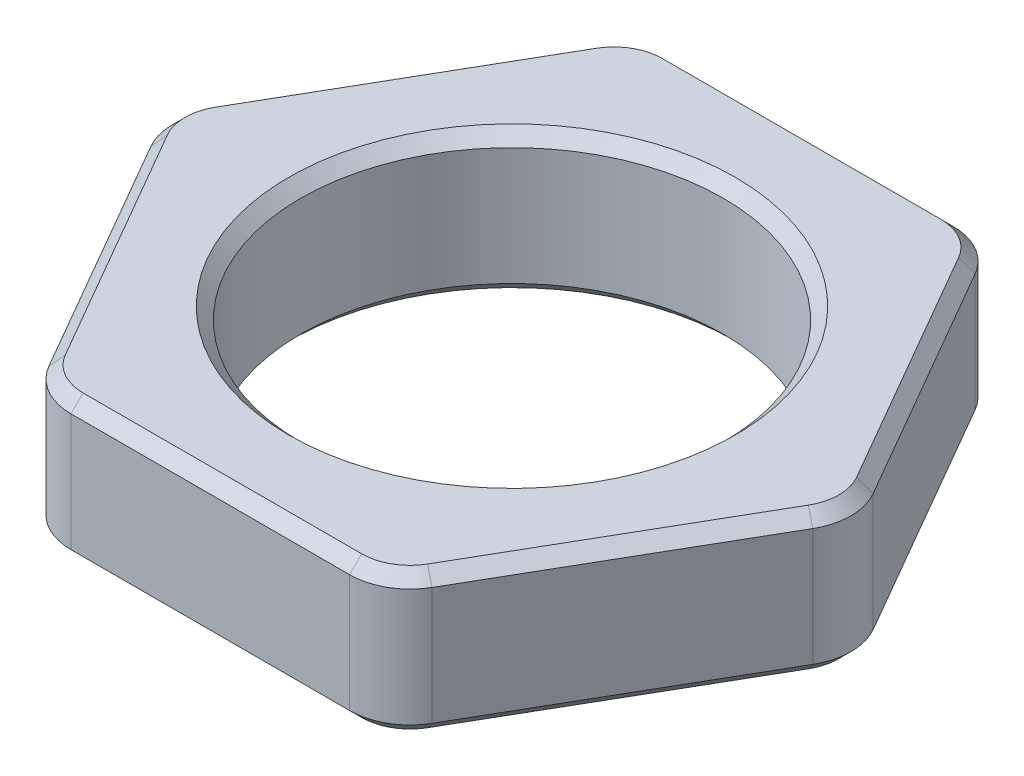
SolidWorks part; units mm, degrees
ref_plane "Front" through (0, 0, 0) normal (0, 0, 1) x (1, 0, 0)
ref_plane "Top" through (0, 0, 0) normal (0, 1, 0) x (1, 0, 0)
ref_plane "Right" through (0, 0, 0) normal (1, 0, 0) x (0, 0, -1)
sketch "Sketch1" plane through (0, 0, 0) normal (0, 1, 0) x (1, 0, 0)
  line L1 (2.8868, 5) -> (-2.8868, 5)
  line L2 (-2.8868, 5) -> (-5.7735, 0)
  line L3 (-5.7735, 0) -> (-2.8868, -5)
  line L4 (-2.8868, -5) -> (2.8868, -5)
  line L5 (2.8868, -5) -> (5.7735, 0)
  line L6 (5.7735, 0) -> (2.8868, 5)
  circle A0 centre (0, 0) radius 5 construction
  circle A1 centre (0, 0) radius 3.5
  dimension "D2" = 7
  dimension "D1" = 10
extrude "Boss-Extrude1" add sketch "Sketch1" along normal mid plane 2.35 contours L2 L3 L4 L5 L6 L1
fillet "Fillet1" radius 1 6 edges at (5.7735, 0, 0) (2.8868, 0, 5) (-5.7735, 0, 0) (-2.8868, 0, -5) (2.8868, 0, -5) (-2.8868, 0, 5)
chamfer "Chamfer1" distance 0.2 angle 45 26 edges at (0, -1.175, 3.5) (2.8094, -1.175, -4.866) (0, -1.175, -5) (-2.8094, -1.175, -4.866) (-4.3301, -1.175, -2.5) (-5.6188, -1.175, 0) (-4.3301, -1.175, 2.5) (-2.8094, -1.175, 4.866) (0, -1.175, 5) (2.8094, -1.175, 4.866) (4.3301, -1.175, 2.5) (5.6188, -1.175, 0) (4.3301, -1.175, -2.5) (0, 1.175, 3.5) (2.8094, 1.175, 4.866) (0, 1.175, 5) (-2.8094, 1.175, 4.866) (-4.3301, 1.175, 2.5) (-5.6188, 1.175, 0) (-4.3301, 1.175, -2.5) (-2.8094, 1.175, -4.866) (0, 1.175, -5) (2.8094, 1.175, -4.866) (4.3301, 1.175, -2.5) (5.6188, 1.175, 0) (4.3301, 1.175, 2.5)
